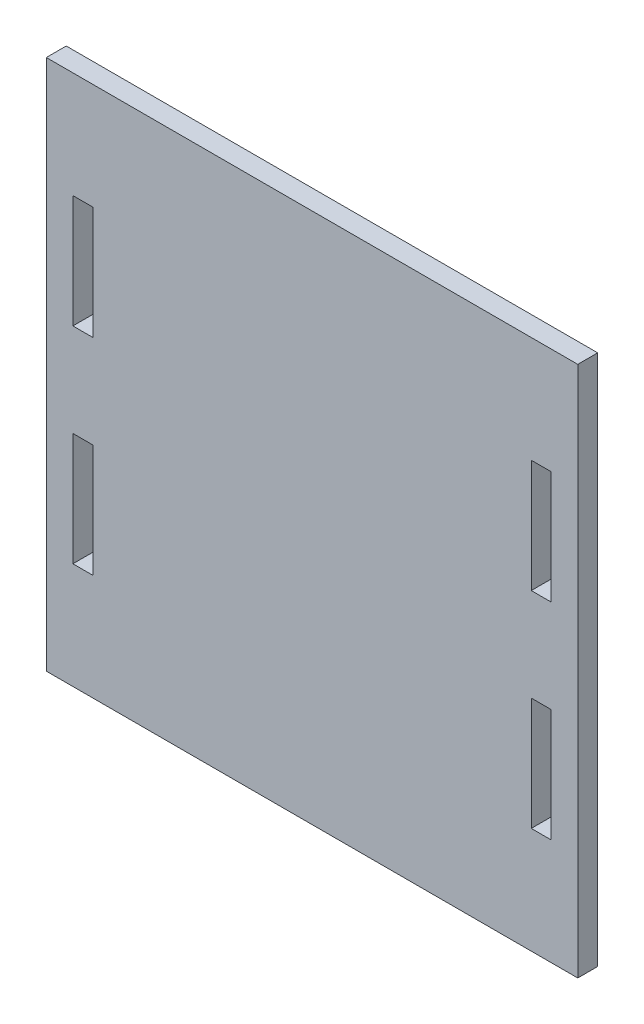
SolidWorks part; units mm, degrees
ref_plane "Front Plane" through (0, 0, 0) normal (0, 0, 1) x (1, 0, 0)
ref_plane "Top Plane" through (0, 0, 0) normal (0, 1, 0) x (1, 0, 0)
ref_plane "Right Plane" through (0, 0, 0) normal (1, 0, 0) x (0, 0, -1)
sketch "Sketch1" plane through (0, 0, 0) normal (0, 0, 1) x (1, 0, 0)
  line L0 (65.8813, 142.5157) -> (127, 142.5157)
  line L1 (0, 15.5157) -> (127, 15.5157)
  line L2 (0, 15.5157) -> (0, 142.5157)
  line L3 (0, 142.5157) -> (61.1188, 142.5157)
  line L4 (127, 15.5157) -> (127, 142.5157)
  line L5 (61.1188, 142.5157) -> (65.8813, 142.5157)
  line L9 (6.35, 117.1157) -> (11.1125, 117.1157)
  line L10 (6.35, 117.1157) -> (6.35, 90.1409)
  line L11 (6.35, 90.1409) -> (11.1125, 90.1409)
  line L12 (11.1125, 117.1157) -> (11.1125, 90.1409)
  line L14 (115.8875, 117.1157) -> (115.8875, 90.1409)
  line L15 (120.65, 90.1409) -> (115.8875, 90.1409)
  line L16 (120.65, 117.1157) -> (120.65, 90.1409)
  line L17 (120.65, 117.1157) -> (115.8875, 117.1157)
  line L18 (120.65, 40.9157) -> (115.8875, 40.9157)
  line L19 (120.65, 40.9157) -> (120.65, 67.8905)
  line L20 (120.65, 67.8905) -> (115.8875, 67.8905)
  line L21 (115.8875, 40.9157) -> (115.8875, 67.8905)
  line L22 (11.1125, 40.9157) -> (11.1125, 67.8905)
  line L23 (6.35, 67.8905) -> (11.1125, 67.8905)
  line L24 (6.35, 40.9157) -> (6.35, 67.8905)
  line L25 (6.35, 40.9157) -> (11.1125, 40.9157)
  dimension "D4" = 4.7625
  dimension "D5" = 25.4
  dimension "D6" = 6.35
extrude "Boss-Extrude1" add sketch "Sketch1" along normal blind 4.7625
